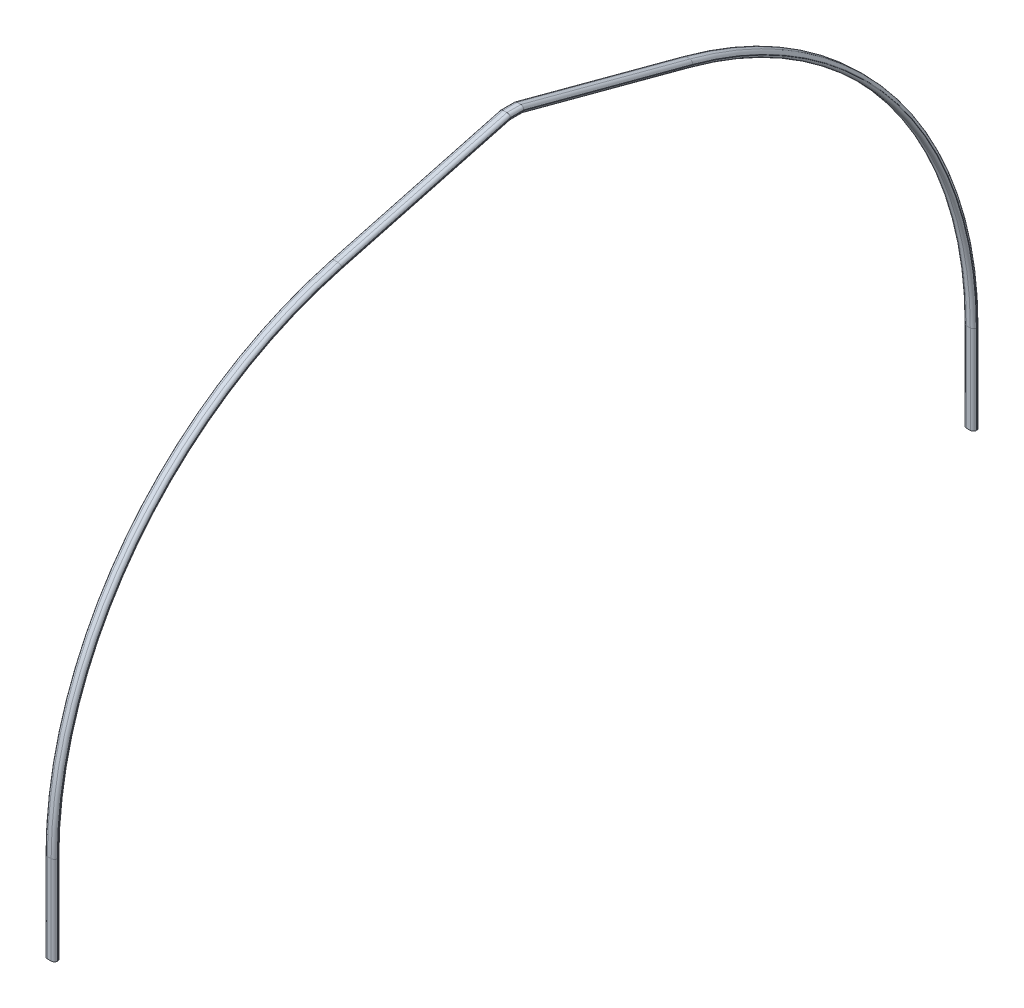
SolidWorks part; units mm, degrees
ref_plane "Front Plane" through (0, 0, 0) normal (0, 0, 1) x (1, 0, 0)
ref_plane "Top Plane" through (0, 0, 0) normal (0, 1, 0) x (1, 0, 0)
ref_plane "Right Plane" through (0, 0, 0) normal (1, 0, 0) x (0, 0, -1)
sketch "Sketch1" plane through (0, 0, 0) normal (0, 1, 0) x (1, 0, 0)
  line L0 (38.1, -31.75) -> (0, -31.75)
  line L3 (0, 0) -> (38.1, 0) construction
  line L4 (0, 20.3048) -> (38.1, 20.3048)
  line L5 (0, -20.3048) -> (38.1, -20.3048)
  line L6 (0, 31.75) -> (38.1, 31.75)
  line L8 (62.23, 2.54) -> (69.7482, 2.54)
  line L12 (62.23, -2.54) -> (62.23, 2.54) construction
  line L14 (62.23, -2.54) -> (69.7482, -2.54)
  line L15 (62.23, 2.54) -> (62.23, -2.54)
  line L16 (-24.13, 2.54) -> (-31.6482, 2.54)
  line L17 (-24.13, 2.54) -> (-24.13, -2.54)
  line L18 (-24.13, -2.54) -> (-31.6482, -2.54)
  arc A2 (0, 20.3048) -> (0, -20.3048) centre (0, 0) ccw
  arc A3 (38.1, -20.3048) -> (38.1, 20.3048) centre (38.1, 0) ccw
  arc A4 (38.1, 31.75) -> (69.7482, 2.54) centre (38.1, 0) cw
  arc A5 (38.1, -31.75) -> (69.7482, -2.54) centre (38.1, 0) ccw construction
  arc A6 (38.1, -31.75) -> (69.7482, -2.54) centre (38.1, 0) ccw
  arc A7 (0, 31.75) -> (-31.6482, 2.54) centre (0, 0) ccw
  arc A8 (0, -31.75) -> (-31.6482, -2.54) centre (0, 0) cw
  point P0 (19.05, -31.75)
  point P3 (19.05, 31.75)
  point P10 (19.05, 0)
  point P20 (0, 0)
  point P21 (0, 0)
sketch "Sketch4" plane through (0, 0, 0) normal (1, 0, 0) x (0, 0, -1)
  line L0 (0, 0) -> (0, 882.8596)
  line L1 (6315.6947, 4564.2147) -> (4637.4463, 5011.7476)
  line L2 (0, 0) -> (4572, 0) construction
  line L3 (4572, 0) -> (4572, 5029.2) construction
  line L4 (2828.3053, 4564.2147) -> (4506.5537, 5011.7476)
  line L5 (9144, 0) -> (9144, 882.8596)
  line L6 (0, 3810) -> (7772.8418, 3810) construction
  line L7 (4506.5537, 5011.7476) -> (4637.4463, 5011.7476)
  arc A0 (0, 882.8596) -> (2828.3053, 4564.2147) centre (3810, 882.8596) cw
  arc A1 (9144, 882.8596) -> (6315.6947, 4564.2147) centre (5334, 882.8596) ccw
  point P8 (0, 3810)
  dimension "D2" = 4572
  dimension "D4" = 3810
  dimension "D1" = 3810
  dimension "D3" = 5029.2
sweep "Sweep1" add profiles "Sketch1" path "Sketch4"
sketch3d "3DSketch1"
  point P0 (24.7024, 4979.9976, -4570.3255)
ref_plane "Plane1" through (0, 4979.9976, 0) normal (0, -1, 0) x (1, 0, 0)
sketch "Sketch5" plane through (0, 4979.9976, 0) normal (0, -1, 0) x (1, 0, 0)
  line L0 (0, -4572) -> (38.1, -4572) construction
  line L1 (0, -4506.5537) -> (0, -4637.4463) construction
  line L2 (38.1, -4633.2857) -> (38.1, -4510.7143) construction
  line L3 (0, -4572) -> (0, -4552.95)
  line L4 (0, -4633.2857) -> (0, -4510.7143) construction
  line L5 (19.05, -4510.7143) -> (19.05, -4633.2857) construction
  line L6 (0, -4510.7143) -> (38.1, -4510.7143) construction
  line L7 (0, -4633.2857) -> (38.1, -4633.2857) construction
  circle A0 centre (0, -4552.95) radius 6.35
  circle A1 centre (38.1, -4552.95) radius 6.35
  circle A2 centre (38.1, -4591.05) radius 6.35
  circle A3 centre (0, -4591.05) radius 6.35
  dimension "D2" = 12.7
  dimension "D1" = 19.05
extrude "Cut-Extrude1" cut sketch "Sketch5" against normal blind 12.7 contours A0 | A1 | A3 | A2
sketch3d "3DSketch2"
  point P0 (25.4087, 4915.0204, -4876.9505)
ref_plane "Plane2" through (0, 5802.8905, -1547.4375) normal (0, -0.9662, 0.2577) x (1, 0, 0)
sketch "Sketch6" plane through (0, 5802.8905, -1547.4375) normal (0, -0.9662, 0.2577) x (-1, 0, 0)
  line L0 (-38.1, 3193.6831) -> (-38.1, 3447.6831)
  line L1 (-38.1, 4926.4172) -> (-38.1, 3193.6831) construction
  line L2 (-38.1, 3447.6831) -> (-38.1, 3655.9631)
  line L3 (-19.05, 3193.6831) -> (-19.05, 3831.7733) construction
  line L4 (0, 3193.6831) -> (-38.1, 3193.6831) construction
  circle A0 centre (-38.1, 3447.6831) radius 6.35
  circle A1 centre (-38.1, 3655.9631) radius 6.35
  circle A2 centre (0, 3655.9631) radius 6.35
  circle A3 centre (0, 3447.6831) radius 6.35
  dimension "D2" = 12.7
  dimension "D4" = 12.7
  dimension "D1" = 254
  dimension "D3" = 208.28
extrude "Cut-Extrude2" cut sketch "Sketch6" against normal blind 12.7 contours A3 | A0 | A2 | A1
